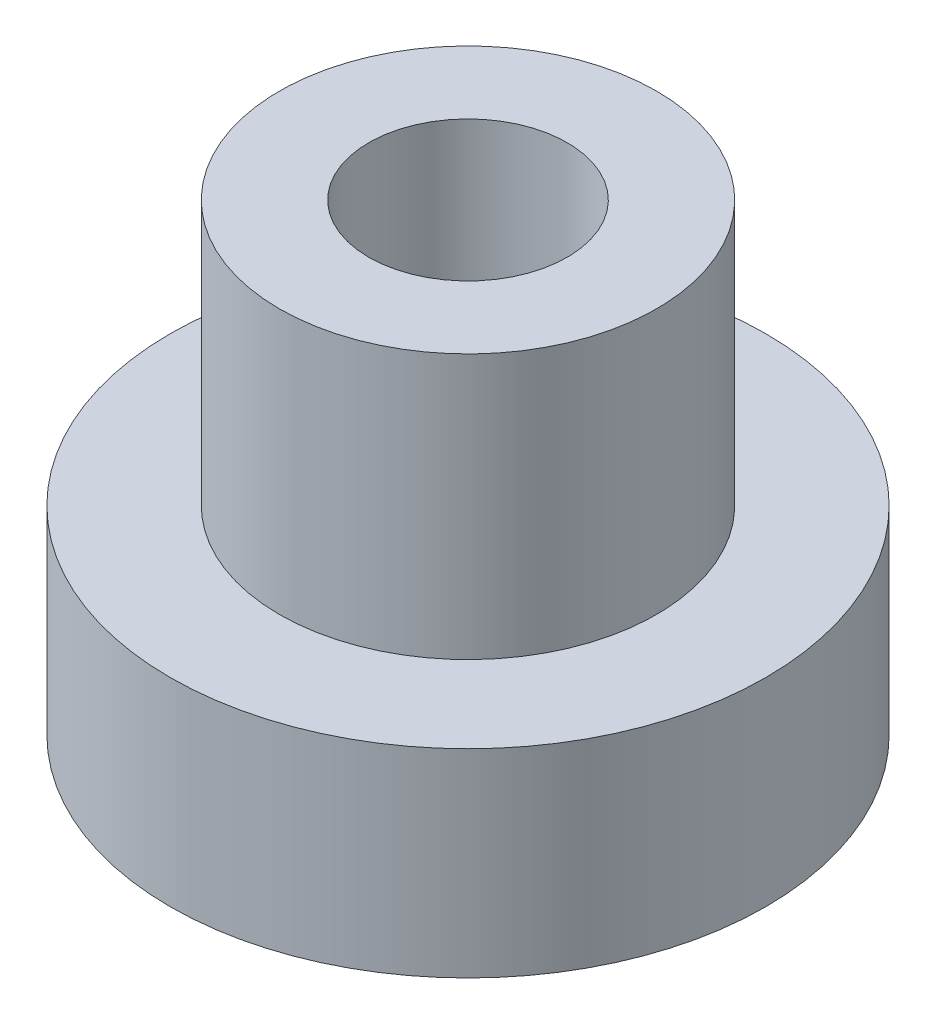
SolidWorks part; units mm, degrees
ref_plane "Front Plane" through (0, 0, 0) normal (0, 0, 1) x (1, 0, 0)
ref_plane "Top Plane" through (0, 0, 0) normal (0, 1, 0) x (1, 0, 0)
ref_plane "Right Plane" through (0, 0, 0) normal (1, 0, 0) x (0, 0, -1)
sketch "Sketch1" plane through (0, 0, 0) normal (0, 1, 0) x (1, 0, 0)
  circle A0 centre (0, 0) radius 4.5
  circle A1 centre (0, 0) radius 1.5
  dimension "D1" = 9
  dimension "D2" = 3
extrude "Boss-Extrude1" add sketch "Sketch1" along normal blind 3
sketch "Sketch2" plane through (0, 3, 0) normal (0, 1, 0) x (1, 0, 0)
  circle A0 centre (0, 0) radius 2.85
  circle A1 centre (0, 0) radius 1.5
  dimension "D1" = 5.7
extrude "Boss-Extrude2" add sketch "Sketch2" along normal blind 4
